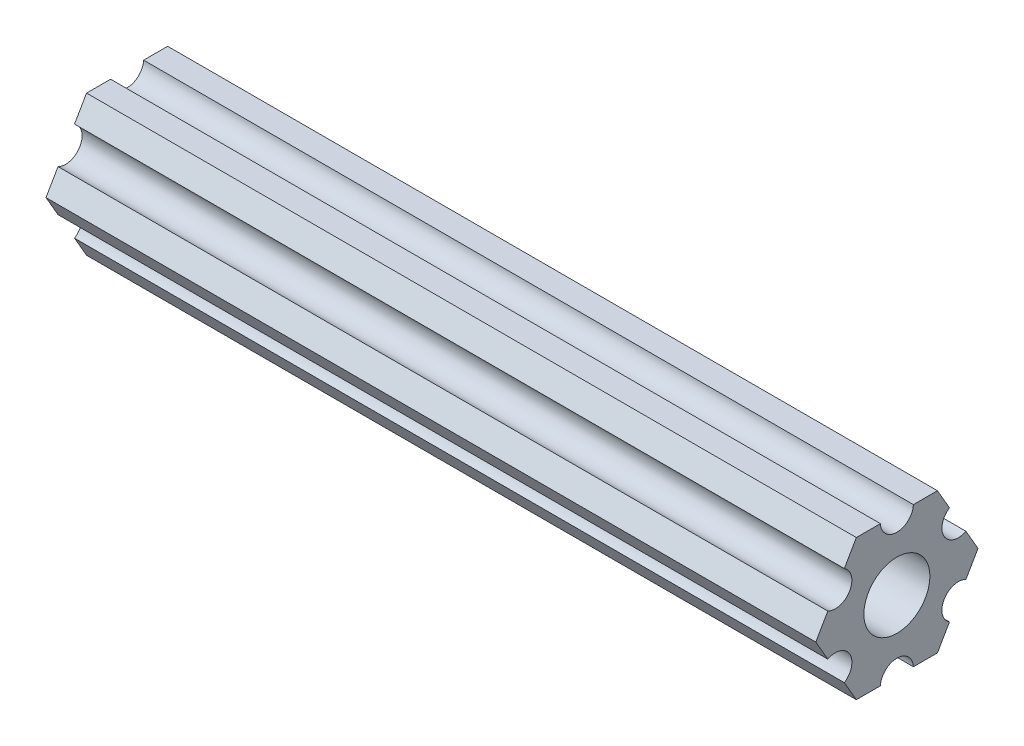
SolidWorks part; units mm, degrees
material "6061 Alloy"
ref_plane "Front Plane" through (0, 0, 0) normal (0, 0, 1) x (1, 0, 0)
ref_plane "Top Plane" through (0, 0, 0) normal (0, 1, 0) x (1, 0, 0)
ref_plane "Right Plane" through (0, 0, 0) normal (1, 0, 0) x (0, 0, -1)
sketch "Sketch2" plane through (0, 0, 0) normal (1, 0, 0) x (0, 0, -1)
  line L0 (-12.5893, 33.4976) -> (1.7674, 33.4976) construction
  line L1 (-1.8218, 39.7142) -> (-3.9504, 39.7142)
  line L2 (-9.0001, 39.7142) -> (-10.0645, 37.8707)
  line L3 (-12.5893, 33.4976) -> (-11.525, 31.6541)
  line L4 (-9.0001, 27.2809) -> (-6.8714, 27.2809)
  line L5 (-1.8218, 27.2809) -> (-0.7574, 29.1244)
  line L6 (1.7674, 33.4976) -> (0.7031, 35.3411)
  line L7 (-6.8714, 39.7142) -> (-9.0001, 39.7142)
  line L8 (-0.7574, 37.8707) -> (-1.8218, 39.7142)
  line L9 (0.7031, 31.6541) -> (1.7674, 33.4976)
  line L10 (-3.9504, 27.2809) -> (-1.8218, 27.2809)
  line L11 (-10.0645, 29.1244) -> (-9.0001, 27.2809)
  line L12 (-11.525, 35.3411) -> (-12.5893, 33.4976)
  circle A0 centre (-5.4109, 33.4976) radius 3.3782 construction
  circle A1 centre (-5.4109, 33.4976) radius 3.3782 construction
  circle A2 centre (-5.4109, 33.4976) radius 6.2167 construction
  arc A3 (-6.8714, 39.7142) -> (-3.9504, 39.7142) centre (-5.4109, 39.7858) ccw
  arc A4 (-6.8714, 27.2809) -> (-3.9504, 27.2809) centre (-5.4109, 27.2093) cw
  arc A5 (0.7031, 31.6541) -> (-0.7574, 29.1244) centre (0.0348, 30.3534) ccw
  arc A6 (-10.0645, 37.8707) -> (-11.525, 35.3411) centre (-10.8567, 36.6417) cw
  arc A7 (-10.0645, 29.1244) -> (-11.525, 31.6541) centre (-10.8567, 30.3534) ccw
  arc A8 (0.7031, 35.3411) -> (-0.7574, 37.8707) centre (0.0348, 36.6417) cw
  circle A9 centre (-5.4109, 33.4976) radius 2.921
  point P30 (-5.4109, 33.4976)
  dimension "D1" = 12.4333
  dimension "D2" = 9.652
  dimension "D5" = 5.842
  dimension "D3" = 2.921
  dimension "D4" = 3
extrude "Boss-Extrude1" add sketch "Sketch2" along normal up to surface (68.128 mm away) from surface contours L6 A8 L8 L1 A3 L7 L2 A6 L12 L3 A7 L11 L4 A4 L10 L5 A5 L9 | A9
